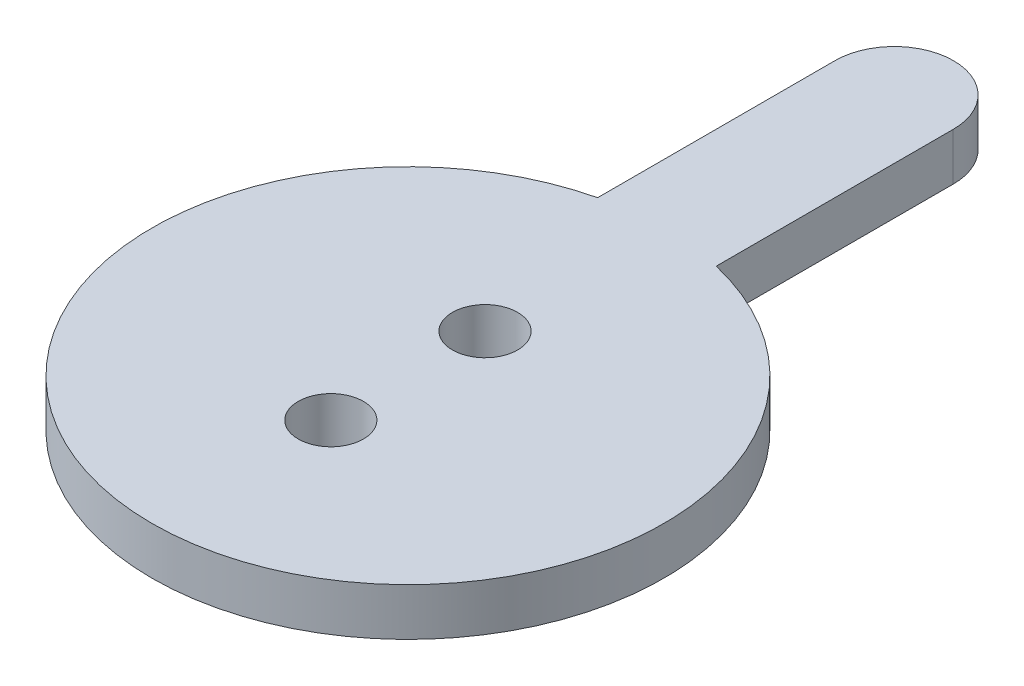
SolidWorks part; units mm, degrees
ref_plane "Front Plane" through (0, 0, 0) normal (0, 0, 1) x (1, 0, 0)
ref_plane "Top Plane" through (0, 0, 0) normal (0, 1, 0) x (1, 0, 0)
ref_plane "Right Plane" through (0, 0, 0) normal (1, 0, 0) x (0, 0, -1)
sketch "Sketch1" plane through (0, 0, 0) normal (0, 1, 0) x (1, 0, 0)
  line L0 (0, 41) -> (0, 21.5809)
  line L1 (4.9996, 20.9938) -> (4.9996, 40.9389)
  line L2 (-5, 40.9937) -> (-5, 20.9937)
  circle A0 centre (0, 0) radius 21.5809
  arc A1 (-5, 40.9937) -> (4.9996, 40.9389) centre (0, 41) cw
  circle A2 centre (0, 6.5) radius 2.75
  circle A3 centre (0, -6.5) radius 2.75
  dimension "D1" = 5
  dimension "D2" = 6.5
  dimension "D3" = 6.5
extrude "Boss-Extrude1" add sketch "Sketch1" along normal blind 4 contours A1 L2 A0 L1 | A0
